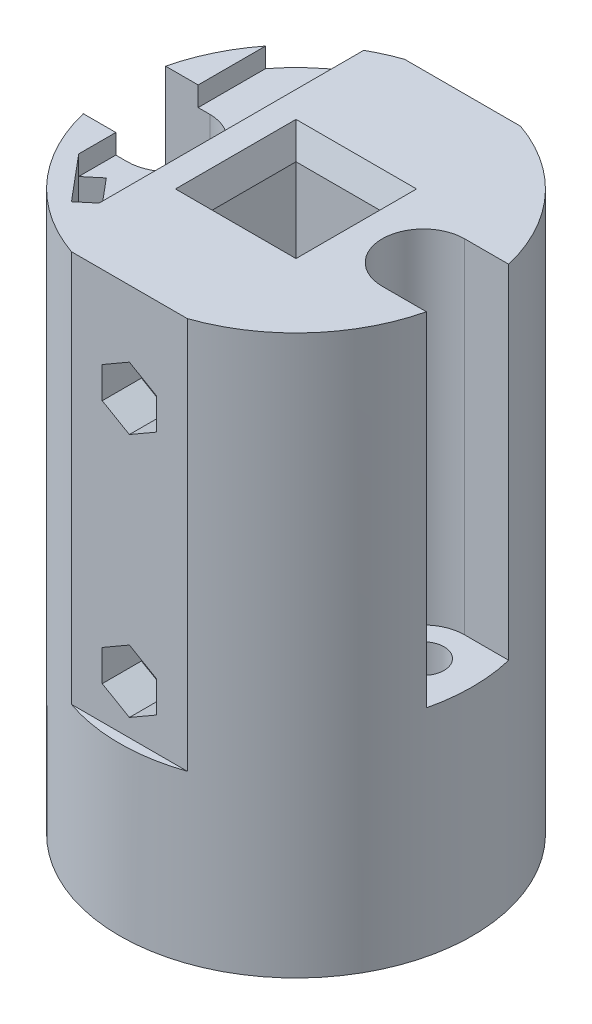
SolidWorks part; units mm, degrees
ref_plane "Спереди" through (0, 0, 0) normal (0, 0, 1) x (1, 0, 0)
ref_plane "Сверху" through (0, 0, 0) normal (0, 1, 0) x (1, 0, 0)
ref_plane "Справа" through (0, 0, 0) normal (1, 0, 0) x (0, 0, -1)
sketch "Sketch1" plane through (0, 0, 0) normal (0, 1, 0) x (1, 0, 0)
  line L0 (0, 0) -> (17.6067, 3.7424) construction
  line L1 (5.15, -5.15) -> (-5.15, -5.15)
  line L2 (5.15, -5.15) -> (5.15, 5.15)
  line L3 (5.15, 5.15) -> (-5.15, 5.15)
  line L4 (-5.15, -5.15) -> (-5.15, 5.15)
  line L5 (5.15, -5.15) -> (-5.15, 5.15) construction
  line L6 (5.15, 5.15) -> (-5.15, -5.15) construction
  line L7 (17.6067, 3.7424) -> (-17.6067, 3.7424) construction
  line L8 (-17.6067, 3.7424) -> (0, 0) construction
  line L9 (-13, 0) -> (13, 0) construction
  circle A0 centre (0, 0) radius 18
  circle A1 centre (13, 0) radius 2.1
  circle A2 centre (-13, 0) radius 2.1
  point P12 (0, 0)
  dimension "D1" = 36
  dimension "D3" = 156
  dimension "D4" = 4.2
  dimension "D2" = 10.3
  dimension "D5" = 26
extrude "Boss-Extrude1" add sketch "Sketch1" along normal blind 57
sketch "Sketch5" plane through (0, 57, 0) normal (0, 1, 0) x (1, 0, 0)
  line L0 (0, 18) -> (0, -18) construction
  line L1 (5.9161, 17) -> (-5.9161, 17)
  line L2 (5.9161, -17) -> (-5.9161, -17)
  circle A0 centre (0, 0) radius 18 construction
  arc A1 (5.9161, 17) -> (-5.9161, 17) centre (0, 0) ccw
  arc A2 (5.9161, -17) -> (-5.9161, -17) centre (0, 0) cw
  point P11 (0, 17)
  dimension "D1" = 1
extrude "Cut-Extrude4" cut sketch "Sketch5" against normal blind 40
sketch "Sketch6" plane through (0, 0, -17) normal (0, 0, -1) x (-1, 0, 0)
  line L0 (0, 57) -> (0, 0) construction
  line L1 (5.9161, 57) -> (-5.9161, 57) construction
  line L2 (5.9161, 17) -> (-5.9161, 17) construction
  line L3 (5.9161, 0) -> (-5.9161, 0) construction
  circle A0 centre (0, 47) radius 1.5
  circle A1 centre (0, 22) radius 1.5
  dimension "D1" = 3
  dimension "D2" = 10
  dimension "D3" = 5
extrude "Cut-Extrude5" cut sketch "Sketch6" against normal through all
sketch "Sketch7" plane through (0, 0, -17) normal (0, 0, -1) x (-1, 0, 0)
  circle A0 centre (0, 47) radius 3
  circle A1 centre (0, 22) radius 3
  dimension "D1" = 6
extrude "Cut-Extrude6" cut sketch "Sketch7" against normal blind 3
sketch "Sketch8" plane through (0, 0, 17) normal (0, 0, 1) x (1, 0, 0)
  line L0 (5.9161, 17) -> (5.9161, 57) construction
  line L1 (0, 43.8) -> (2.7713, 45.4)
  line L2 (2.7713, 45.4) -> (2.7713, 48.6)
  line L3 (2.7713, 48.6) -> (0, 50.2)
  line L4 (0, 50.2) -> (-2.7713, 48.6)
  line L5 (-2.7713, 48.6) -> (-2.7713, 45.4)
  line L6 (-2.7713, 45.4) -> (0, 43.8)
  line L9 (0, 18.8) -> (2.7713, 20.4)
  line L10 (2.7713, 20.4) -> (2.7713, 23.6)
  line L11 (2.7713, 23.6) -> (0, 25.2)
  line L12 (0, 25.2) -> (-2.7713, 23.6)
  line L13 (-2.7713, 23.6) -> (-2.7713, 20.4)
  line L14 (-2.7713, 20.4) -> (0, 18.8)
  circle A0 centre (0, 47) radius 3.2 construction
  circle A1 centre (0, 22) radius 3.2 construction
  dimension "D1" = 6.4
extrude "Cut-Extrude7" cut sketch "Sketch8" against normal blind 4
chamfer "Chamfer1" distance 1 angle 70 4 edges at (-5.15, 57, 0) (0, 57, -5.15) (0, 57, 5.15) (5.15, 57, 0)
sketch "Sketch9" plane through (0, 0, 0) normal (0, -1, 0) x (1, 0, 0)
  line L0 (0, 0) -> (17.6067, -3.7424) construction
  line L1 (17.6067, -3.7424) -> (-17.6067, -3.7424) construction
  line L2 (-17.6067, -3.7424) -> (0, 0) construction
  line L4 (5.15, -5.15) -> (-5.15, -5.15) construction
  line L5 (15.4383, -3.3582) -> (9.4066, -2.0761)
  line L6 (-9.4588, -2.1639) -> (-15.3549, -3.4171)
  circle A0 centre (-13, 0) radius 4.15 construction
  circle A1 centre (13, 0) radius 4.15 construction
  circle A3 centre (0, 0) radius 18 construction
  arc A4 (15.4383, -3.3582) -> (9.4066, -2.0761) centre (13, 0) ccw
  arc A5 (-9.4588, -2.1639) -> (-15.3549, -3.4171) centre (-13, 0) ccw
  dimension "D1" = 8.3
  dimension "D2" = 156
extrude "Cut-Extrude9" cut sketch "Sketch9" against normal blind 6
chamfer "Chamfer2" distance 0.5 angle 70 4 edges at (-13.8628, 0, 4.0593) (-12.4069, 0, -2.7905) (13.8628, 0, 4.0593) (12.4225, 0, -2.7171)
sketch "Sketch10" plane through (0, 57, 0) normal (0, 1, 0) x (1, 0, 0)
  line L0 (13, 4.2) -> (21, 4.2)
  line L1 (21, 4.2) -> (21, -4.2)
  line L2 (21, -4.2) -> (13, -4.2)
  line L3 (-13, 4.2) -> (-21, 4.2)
  line L4 (-21, 4.2) -> (-21, -4.2)
  line L5 (-13, -4.2) -> (-21, -4.2)
  circle A0 centre (13, 0) radius 4.2 construction
  circle A1 centre (-13, 0) radius 4.2 construction
  arc A2 (13, 4.2) -> (13, -4.2) centre (13, 0) ccw
  arc A3 (-13, 4.2) -> (-13, -4.2) centre (-13, 0) cw
  dimension "D1" = 8.4
  dimension "D2" = 8
extrude "Cut-Extrude10" cut sketch "Sketch10" against normal blind 35
sketch "Sketch11" plane through (0, 0, 0) normal (0, -1, 0) x (1, 0, 0)
  line L0 (0, 0) -> (0, 18) construction
  line L1 (0, 0) -> (-13.7888, 11.5702) construction
  line L2 (-14.1851, 7.9865) -> (-10.3283, 12.5827)
  line L3 (-14.1851, 7.9865) -> (-12.653, 6.7009)
  line L4 (-10.3283, 12.5827) -> (-8.7963, 11.2972)
  line L5 (-12.653, 6.7009) -> (-8.7963, 11.2972)
  line L6 (-14.1851, 7.9865) -> (-8.7963, 11.2972) construction
  line L7 (-10.3283, 12.5827) -> (-12.653, 6.7009) construction
  circle A0 centre (0, 0) radius 18 construction
  point P8 (-11.4907, 9.6418)
  dimension "D1" = 50
  dimension "D2" = 6
  dimension "D3" = 2
  dimension "D4" = 3
extrude "Cut-Extrude11" cut sketch "Sketch11" against normal through all
chamfer "Chamfer3" distance 0.5 angle 70 4 edges at (-13.419, 0, 7.3437) (-12.2567, 0, 10.2846) (-10.7246, 0, 8.999) (-9.5623, 0, 11.9399)
sketch "Sketch13" plane through (0, 57, 0) normal (0, 1, 0) x (1, 0, 0)
  line L0 (-8.7963, -11.2972) -> (-8.7963, 15.7043)
  line L1 (-14.1851, -7.9865) -> (-14.1851, 11.0808)
  line L4 (-14.1851, -7.9865) -> (-8.7963, -11.2972)
  arc A1 (-5.9161, 17) -> (-17.5031, 4.2) centre (0, 0) ccw construction
  arc A2 (-8.7963, 15.7043) -> (-14.1851, 11.0808) centre (0, 0) ccw
extrude "Cut-Extrude13" cut sketch "Sketch13" against normal blind 2
